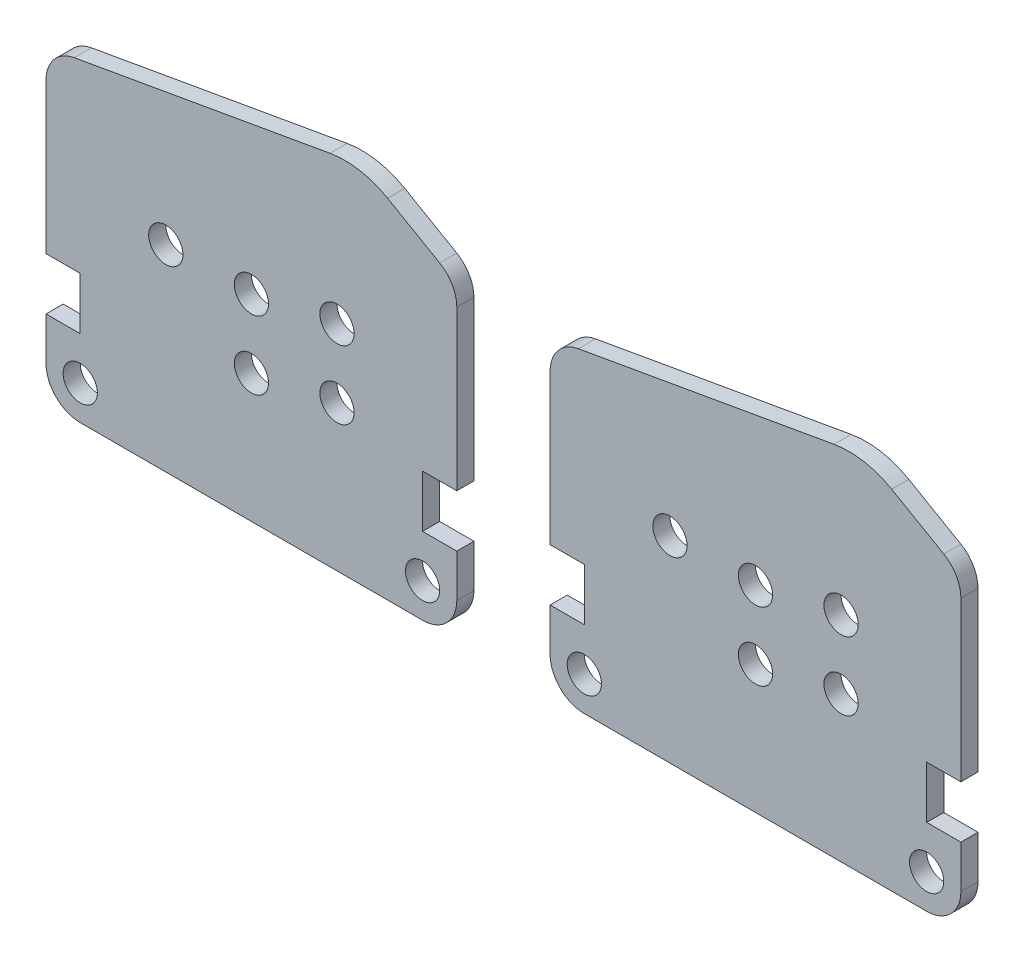
SolidWorks part; units mm, degrees
ref_plane "前视基准面" through (0, 0, 0) normal (0, 0, 1) x (1, 0, 0)
ref_plane "上视基准面" through (0, 0, 0) normal (0, 1, 0) x (1, 0, 0)
ref_plane "右视基准面" through (0, 0, 0) normal (1, 0, 0) x (0, 0, -1)
sketch "Model" plane through (0, 0, 0) normal (0, 0, 1) x (1, 0, 0)
  line L0 (37.8637, 15.9529) -> (37.8637, 18.4529)
  line L1 (35.8637, 13.9529) -> (15.8637, 13.9529)
  line L2 (13.8637, 15.9529) -> (13.8637, 18.4529)
  line L3 (13.8637, 21.5029) -> (13.8637, 30.2747)
  line L4 (15.5164, 32.2443) -> (30.4565, 34.8787)
  line L5 (33.8248, 34.2848) -> (36.8637, 32.5302)
  line L6 (37.8637, 30.7982) -> (37.8637, 21.5029)
  line L7 (15.8637, 21.4529) -> (15.8637, 18.4529)
  line L8 (13.8637, 18.4529) -> (15.8637, 18.4529)
  line L9 (35.8637, 21.4529) -> (35.8637, 18.4529)
  line L10 (35.8637, 18.4529) -> (37.8637, 18.4529)
  line L11 (15.8637, 21.4529) -> (15.8637, 21.5029)
  line L12 (15.8637, 21.5029) -> (13.8637, 21.5029)
  line L13 (35.8637, 21.5029) -> (37.8637, 21.5029)
  line L14 (35.8637, 21.4529) -> (35.8637, 21.5029)
  line L15 (67.3144, 15.9529) -> (67.3144, 18.4529)
  line L16 (65.3144, 13.9529) -> (45.3144, 13.9529)
  line L17 (43.3144, 15.9529) -> (43.3144, 18.4529)
  line L18 (43.3144, 21.5029) -> (43.3144, 30.2747)
  line L19 (44.9671, 32.2443) -> (59.9073, 34.8787)
  line L20 (63.2755, 34.2848) -> (66.3144, 32.5302)
  line L21 (67.3144, 30.7982) -> (67.3144, 21.5029)
  line L22 (45.3144, 21.4529) -> (45.3144, 18.4529)
  line L23 (43.3144, 18.4529) -> (45.3144, 18.4529)
  line L24 (65.3144, 21.4529) -> (65.3144, 18.4529)
  line L25 (65.3144, 18.4529) -> (67.3144, 18.4529)
  line L26 (45.3144, 21.4529) -> (45.3144, 21.5029)
  line L27 (45.3144, 21.5029) -> (43.3144, 21.5029)
  line L28 (65.3144, 21.5029) -> (67.3144, 21.5029)
  line L29 (65.3144, 21.4529) -> (65.3144, 21.5029)
  circle A0 centre (35.8637, 15.9529) radius 1
  circle A1 centre (15.8637, 15.9529) radius 1
  circle A2 centre (25.8637, 25.4529) radius 1
  circle A3 centre (20.8637, 25.4529) radius 1
  circle A4 centre (30.8637, 26.4529) radius 1
  circle A5 centre (25.8637, 21.4529) radius 1
  circle A6 centre (30.8637, 22.4529) radius 1
  circle A7 centre (65.3144, 15.9529) radius 1
  circle A8 centre (45.3144, 15.9529) radius 1
  circle A9 centre (55.3144, 25.4529) radius 1
  circle A10 centre (50.3144, 25.4529) radius 1
  circle A11 centre (60.3144, 26.4529) radius 1
  circle A12 centre (55.3144, 21.4529) radius 1
  circle A13 centre (60.3144, 22.4529) radius 1
  arc A14 (35.8637, 13.9529) -> (37.8637, 15.9529) centre (35.8637, 15.9529) ccw
  arc A15 (13.8637, 15.9529) -> (15.8637, 13.9529) centre (15.8637, 15.9529) ccw
  arc A16 (15.5164, 32.2443) -> (13.8637, 30.2747) centre (15.8637, 30.2747) ccw
  arc A17 (33.8248, 34.2848) -> (30.4565, 34.8787) centre (31.3248, 29.9546) ccw
  arc A18 (37.8637, 30.7982) -> (36.8637, 32.5302) centre (35.8637, 30.7982) ccw
  arc A19 (65.3144, 13.9529) -> (67.3144, 15.9529) centre (65.3144, 15.9529) ccw
  arc A20 (43.3144, 15.9529) -> (45.3144, 13.9529) centre (45.3144, 15.9529) ccw
  arc A21 (44.9671, 32.2443) -> (43.3144, 30.2747) centre (45.3144, 30.2747) ccw
  arc A22 (63.2755, 34.2848) -> (59.9073, 34.8787) centre (60.7755, 29.9546) ccw
  arc A23 (67.3144, 30.7982) -> (66.3144, 32.5302) centre (65.3144, 30.7982) ccw
  spline S0 degree 3 poles (0, 0) (0.3333, 0) (0.6667, 0) (1, 0) knots 0 0 0 0 1 1 1 1
  spline S1 degree 3 poles (0, 0) (0.3333, 0) (0.6667, 0) (1, 0) knots 0 0 0 0 1 1 1 1
extrude "凸台-拉伸1" add sketch "Model" along normal blind 1 contours S0 S1 | A6 | A5 | A4 | A3 | A2 | A1 | A0 | A13 | A12 | A11 | A10 | A9 | A8 | A7 | L0 L10 L9 L14 L13 L6 A18 L5 A17 L4 A16 L3 L12 L11 L7 L8 L2 A15 L1 A14 | L15 L25 L24 L29 L28 L21 A23 L20 A22 L19 A21 L18 L27 L26 L22 L23 L17 A20 L16 A19
